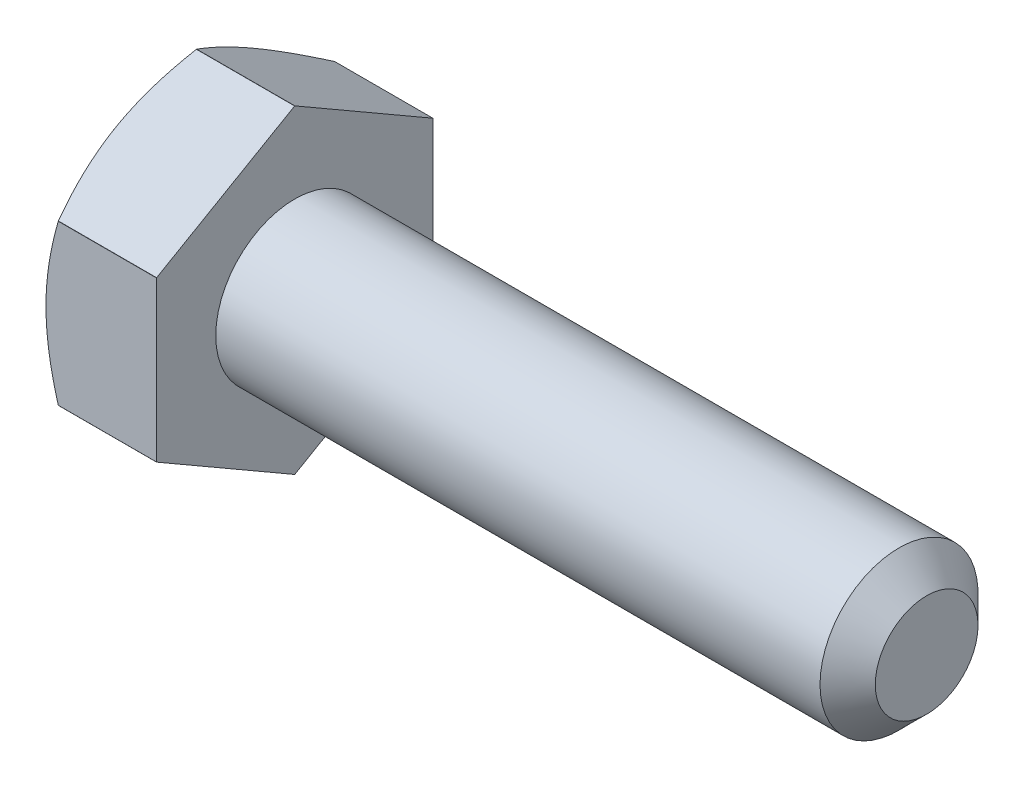
SolidWorks part; units mm, degrees
ref_plane "Спереди" through (0, 0, 0) normal (0, 0, 1) x (1, 0, 0)
ref_plane "Сверху" through (0, 0, 0) normal (0, 1, 0) x (1, 0, 0)
ref_plane "Справа" through (0, 0, 0) normal (1, 0, 0) x (0, 0, -1)
sketch "Эскиз1" plane through (0, 0, 0) normal (0, 0, 1) x (1, 0, 0)
  line L0 (-21.7003, 0) -> (27.3657, 0) construction
  line L1 (-12.8, 0) -> (-12.8, 4.04)
  line L2 (-12.8, 4.04) -> (-10, 4.04)
  line L3 (-10, 4.04) -> (-10, 2)
  line L4 (-10, 2) -> (6, 2)
  line L5 (6, 2) -> (6, 0)
  line L6 (6, 0) -> (-12.8, 0)
  dimension "D1" = 4.04
  dimension "D2" = 2.8
  dimension "D3" = 2
  dimension "D4" = 16
  dimension "D5" = 6
revolve "Повернуть1" add sketch "Эскиз1" angle 360 about L0
sketch "Эскиз2" plane through (-12.8, 0, 0) normal (-1, 0, 0) x (0, 0, 1)
  line L1 (0, 4.0415) -> (-3.5, 2.0207)
  line L2 (-3.5, 2.0207) -> (-3.5, -2.0207)
  line L3 (-3.5, -2.0207) -> (0, -4.0415)
  line L4 (0, -4.0415) -> (3.5, -2.0207)
  line L5 (3.5, -2.0207) -> (3.5, 2.0207)
  line L6 (3.5, 2.0207) -> (0, 4.0415)
  circle A0 centre (0, 0) radius 3.5 construction
  dimension "D1" = 7
extrude "Вырез-Вытянуть1" cut sketch "Эскиз2" against normal up to next (18.8 mm away) flip side to cut
chamfer "Фаска1" distance 0.7 angle 45 1 edges at (6, 0, 2)
ref_plane "Плоскость1" through (0, 0, 0) normal (0, 0.5, -0.866) x (-1, 0, 0)
sketch "Эскиз5" plane through (0, 0, 0) normal (0, 0.5, -0.866) x (-1, 0, 0)
  line L2 (0, 0) -> (16.7708, 0) construction
  line L4 (12.8, 3.4975) -> (12.8, 6.4975)
  line L5 (12.8, 6.4975) -> (11.0679, 6.4975)
  line L6 (11.0679, 6.4975) -> (12.8, 3.4975)
  dimension "D1" = 3
  dimension "D2" = 30
revolve "Вырез-Повернуть1" cut sketch "Эскиз5" angle 360 about L2
